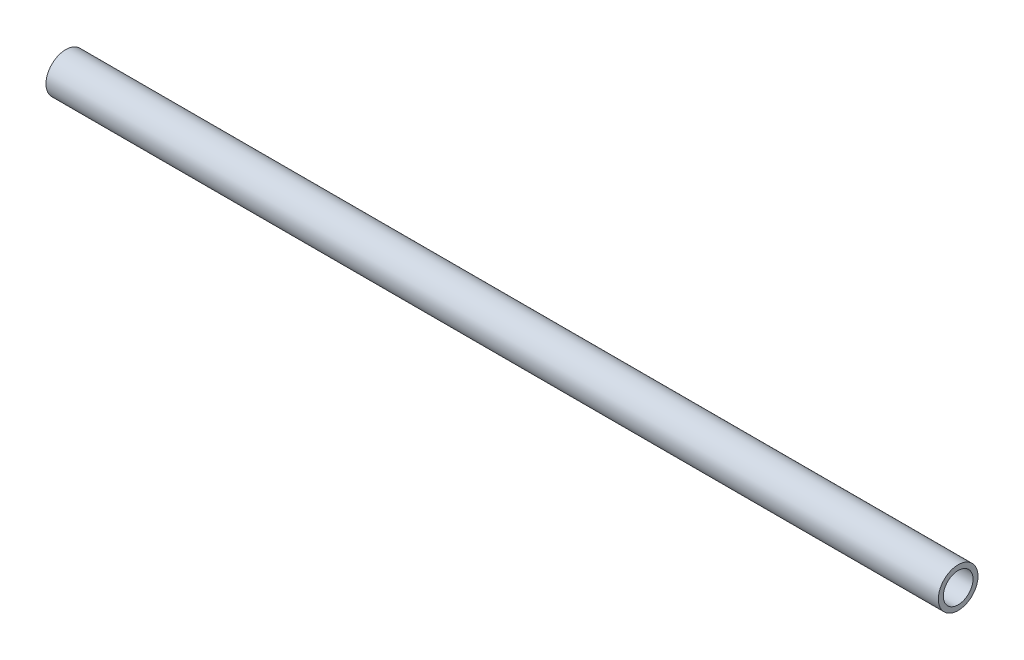
SolidWorks part; units mm, degrees
material "1.0037 (S235JR)"
ref_plane "Front Plane" through (0, 0, 0) normal (0, 0, 1) x (1, 0, 0)
ref_plane "Top Plane" through (0, 0, 0) normal (0, 1, 0) x (1, 0, 0)
ref_plane "Right Plane" through (0, 0, 0) normal (1, 0, 0) x (0, 0, -1)
sketch "Sketch2" plane through (0, 0, 0) normal (1, 0, 0) x (0, 0, -1)
  circle A0 centre (0, 0) radius 8
  circle A1 centre (0, 0) radius 6
  dimension "D1" = 16
  dimension "D2" = 2
extrude "Boss-Extrude2" add sketch "Sketch2" along normal mid plane 360
